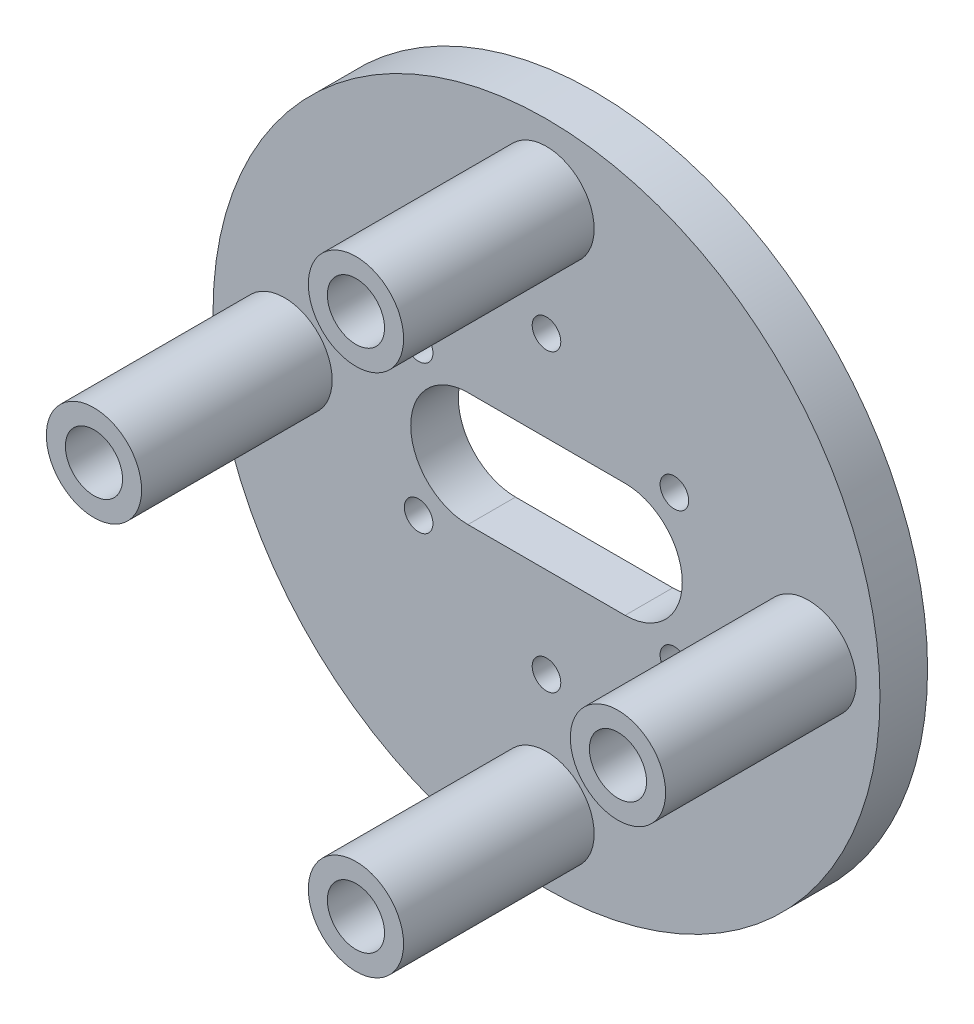
SolidWorks part; units mm, degrees
ref_plane "Plano frontal" through (0, 0, 0) normal (0, 0, 1) x (1, 0, 0)
ref_plane "Plano superior" through (0, 0, 0) normal (0, 1, 0) x (1, 0, 0)
ref_plane "Plano direito" through (0, 0, 0) normal (1, 0, 0) x (0, 0, -1)
sketch "Esboço1" plane through (0, 0, 0) normal (0, 0, 1) x (1, 0, 0)
  circle A0 centre (0, 0) radius 35
  dimension "D1" = 70
extrude "Ressalto-extrusão1" add sketch "Esboço1" along normal blind 5
sketch "Esboço2" plane through (0, 0, 5) normal (0, 0, 1) x (1, 0, 0)
  circle A1 centre (27.5, 0) radius 5
  circle A2 centre (0, -27.5) radius 5
  circle A3 centre (0, 27.5) radius 5
  circle A4 centre (-27.5, 0) radius 5
  dimension "D1" = 10
  dimension "D2" = 10
  dimension "D3" = 10
  dimension "D4" = 10
extrude "Ressalto-extrusão2" add sketch "Esboço2" along normal blind 20
sketch "Esboço3" plane through (0, 0, 25) normal (0, 0, 1) x (1, 0, 0)
  circle A0 centre (0, 27.5) radius 3
  circle A1 centre (27.5, 0) radius 3
  circle A2 centre (0, -27.5) radius 3
  circle A3 centre (-27.5, 0) radius 3
  dimension "D1" = 6
  dimension "D2" = 6
  dimension "D3" = 6
  dimension "D4" = 6
extrude "Corte-extrusão1" cut sketch "Esboço3" against normal blind 5
sketch "Esboço4" plane through (0, 0, 5) normal (0, 0, 1) x (1, 0, 0)
  line L0 (8.25, 6) -> (-8.25, 6)
  line L1 (8.25, -6) -> (-8.25, -6)
  arc A0 (8.25, -6) -> (8.25, 6) centre (8.25, 0) ccw
  arc A1 (-8.25, 6) -> (-8.25, -6) centre (-8.25, 0) ccw
  point P0 (0, 0)
  dimension "D1" = 12
  dimension "D2" = 12
  dimension "D4" = 8.25
  dimension "D3" = 8.25
extrude "Corte-extrusão2" cut sketch "Esboço4" against normal blind 14
sketch "Esboço5" plane through (0, 0, 5) normal (0, 0, 1) x (1, 0, 0)
  circle A6 centre (13.4234, 7.75) radius 1.5
  circle A7 centre (13.4234, -7.75) radius 1.5
  circle A8 centre (0, -15.5) radius 1.5
  circle A9 centre (-13.4234, -7.75) radius 1.5
  circle A10 centre (-13.4234, 7.75) radius 1.5
  circle A11 centre (0, 15.5) radius 1.5
  point P3 (0, -15.5)
  point P8 (-13.4234, -7.75)
  point P10 (-13.4234, 7.75)
  point P12 (0, 15.5)
  point P14 (13.4234, 7.75)
  point P16 (13.4234, -7.75)
  point P17 (0, 0)
  dimension "D3" = 3
  dimension "D4" = 3
  dimension "D5" = 3
  dimension "D6" = 3
  dimension "D7" = 3
  dimension "D8" = 3
  dimension "D2" = 6
extrude "Corte-extrusão3" cut sketch "Esboço5" against normal blind 14
